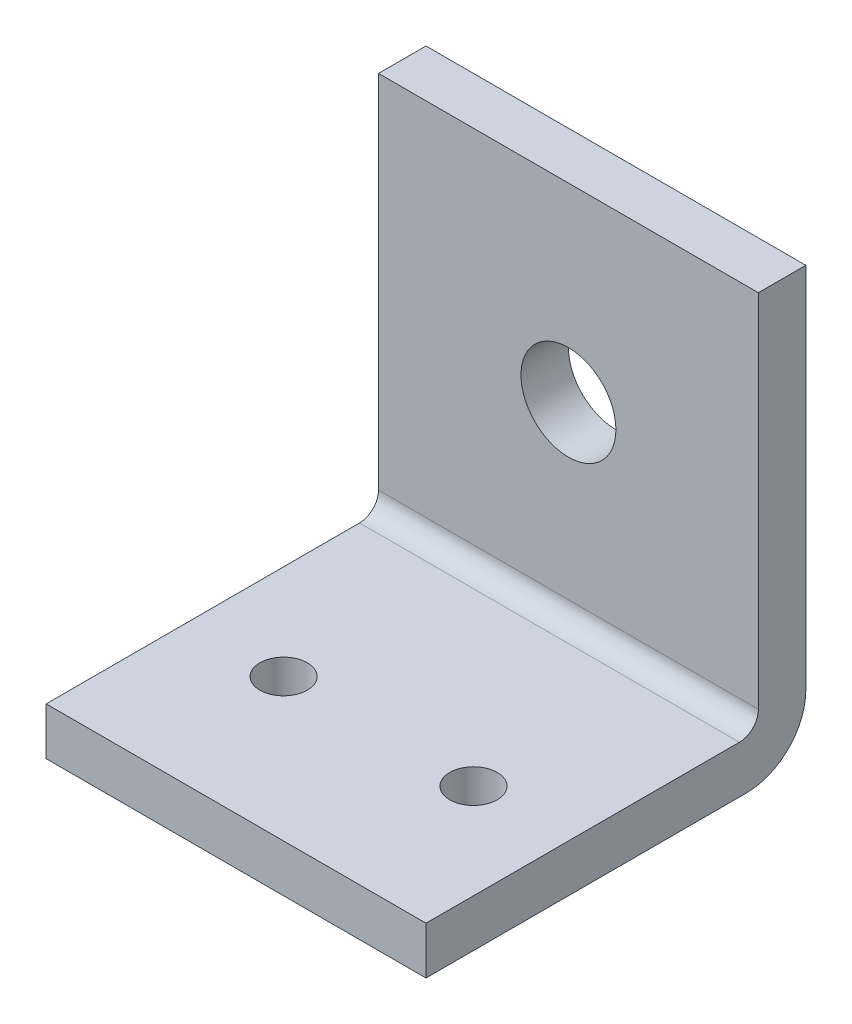
SolidWorks part; units mm, degrees
ref_plane "Front Plane" through (0, 0, 0) normal (0, 0, 1) x (1, 0, 0)
ref_plane "Top Plane" through (0, 0, 0) normal (0, 1, 0) x (1, 0, 0)
ref_plane "Right Plane" through (0, 0, 0) normal (1, 0, 0) x (0, 0, -1)
sketch "Sketch2" plane through (0, 0, 0) normal (0, 0, 1) x (1, 0, 0)
  line L1 (0, 0) -> (40, 0)
  line L2 (0, 0) -> (0, 5)
  line L3 (0, 5) -> (40, 5)
  line L4 (40, 0) -> (40, 5)
  dimension "D1" = 40
  dimension "D2" = 5
extrude "Boss-Extrude1" add sketch "Sketch2" along normal blind 40
sketch "Sketch3" plane through (0, 5, 0) normal (0, 1, 0) x (1, 0, 0)
  line L0 (40, -40) -> (40, 0) construction
  line L1 (0, 0) -> (40, 0)
  line L2 (0, 0) -> (0, -5)
  line L3 (0, -5) -> (40, -5)
  line L4 (40, 0) -> (40, -5)
  dimension "D1" = 5
extrude "Boss-Extrude2" add sketch "Sketch3" along normal blind 40
sketch "Sketch4" plane through (0, 5, 0) normal (0, 1, 0) x (1, 0, 0)
  line L0 (-9.576, -25) -> (47.819, -25) construction
  line L1 (40, -40) -> (0, -40) construction
  line L2 (0, -40) -> (0, -5) construction
  circle A0 centre (10, -25) radius 2.5
  circle A1 centre (30, -25) radius 2.5
  dimension "D2" = 5
  dimension "D1" = 15
  dimension "D3" = 10
  dimension "D5" = 30
  dimension "D4" = 2
extrude "Cut-Extrude1" cut sketch "Sketch4" against normal blind 10
sketch "Sketch5" plane through (0, 0, 5) normal (0, 0, 1) x (1, 0, 0)
  line L0 (0, 0) -> (40, 0) construction
  line L1 (40, 45) -> (40, 5) construction
  circle A0 centre (20, 25) radius 5
  dimension "D1" = 10
  dimension "D2" = 25
  dimension "D3" = 20
extrude "Cut-Extrude2" cut sketch "Sketch5" against normal blind 10
fillet "Fillet1" radius 6.25 1 edges at (20, 0, 0)
fillet "Fillet2" radius 2 1 edges at (20, 5, 5)
